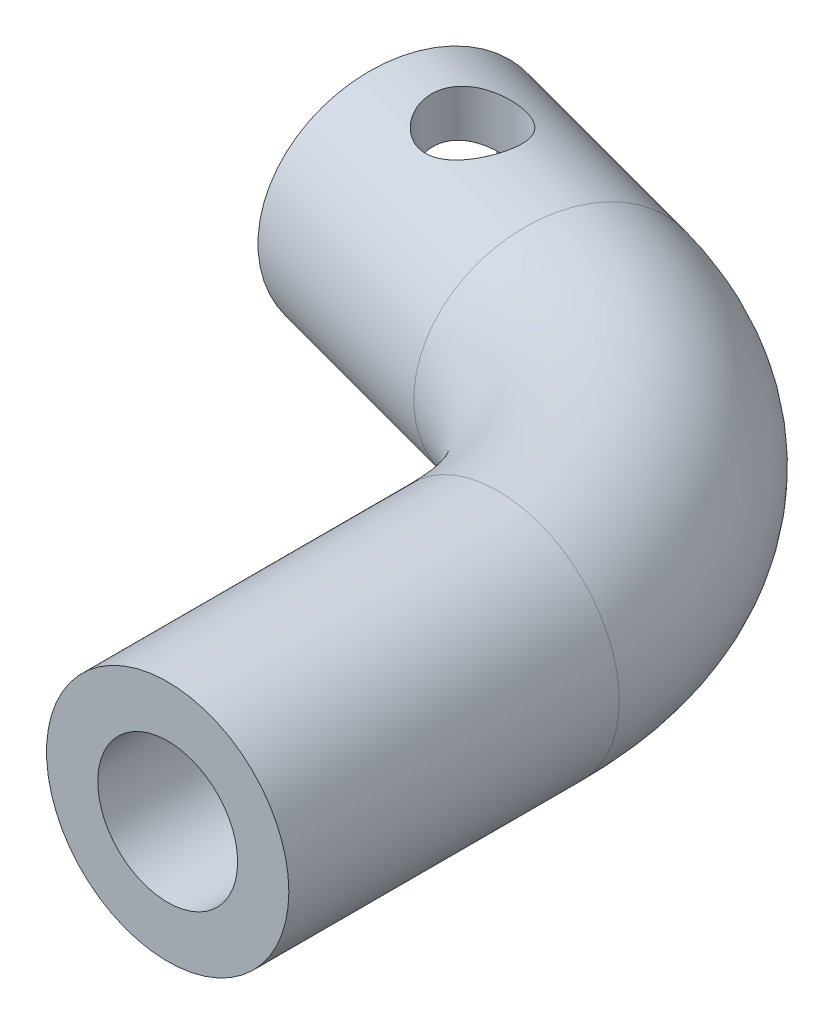
SolidWorks part; units mm, degrees
ref_plane "Front Plane" through (0, 0, 0) normal (0, 0, 1) x (1, 0, 0)
ref_plane "Top Plane" through (0, 0, 0) normal (0, 1, 0) x (1, 0, 0)
ref_plane "Right Plane" through (0, 0, 0) normal (1, 0, 0) x (0, 0, -1)
sketch "PROFILE" plane through (0, 0, 0) normal (0, 1, 0) x (1, 0, 0)
  line L0 (2.5, -10) -> (2.5, -25)
  line L1 (-7.0867, 2.4936) -> (-16.7459, 5.0818)
  line L2 (0, 0) -> (-28.2539, 0) construction
  arc A0 (2.5, -10) -> (-7.0867, 2.4936) centre (-10.4343, -10) ccw
  dimension "D1" = 15
  dimension "D2" = 10
  dimension "D3" = 2.5
  dimension "D4" = 17.5
  dimension "D5" = 15
  dimension "D6" = 25
ref_plane "Plane1" through (0, 0, 25) normal (0, 0, 1) x (1, 0, 0)
sketch "Sketch4" plane through (0, 0, 25) normal (0, 0, 1) x (1, 0, 0)
  circle A0 centre (2.5, 0) radius 5.5
  point P4 (0, 0)
  point P6 (0, 0)
  dimension "D1" = 11
sweep "Sweep2" add profiles "Sketch4" path "PROFILE"
sketch "Sketch6" plane through (0, 0, 25) normal (0, 0, 1) x (1, 0, 0)
  circle A0 centre (2.5, 0) radius 3.175
extrude "HOLE_SHAFT" cut sketch "Sketch6" against normal blind 10
sketch "Sketch7" plane through (-16.8946, 0, -4.5269) normal (-0.9659, 0, -0.2588) x (-0.2588, 0, 0.9659)
  line L0 (9.0122, 0) -> (-0.5744, 0) construction
  circle A0 centre (-0.5744, 0) radius 3.4
  point P3 (0, 0)
  point P4 (-0.5744, 0)
extrude "HOLE_POT" cut sketch "Sketch7" against normal blind 10
sketch "Sketch8" plane through (0, 0, 0) normal (0, 1, 0) x (1, 0, 0)
  line L0 (-7.0867, 2.4936) -> (-16.7459, 5.0818) construction
  circle A0 centre (-12.6435, 3.9825) radius 2
extrude "HOLE_INSERT" cut sketch "Sketch8" along normal through all
sketch "Sketch9" plane through (-7.2353, 0, -1.9387) normal (-0.9659, 0, -0.2588) x (-0.2588, 0, 0.9659)
  line L0 (-2.2229, 2.9736) -> (1.8712, -2.3619) construction
  line L1 (-2.2229, 2.9736) -> (2.4526, -1.5483)
  line L3 (-3.0167, 2.3654) -> (1.8712, -2.3619)
  line L5 (-0.5744, 0) -> (-4.9947, 0) construction
  circle A0 centre (-0.5744, 0) radius 3.4 construction
  arc A1 (-2.2229, 2.9736) -> (-3.0167, 2.3654) centre (-0.5744, 0) ccw
  arc A2 (1.8712, -2.3619) -> (2.4526, -1.5483) centre (-0.5744, 0) ccw
  dimension "D1" = 1
  dimension "D2" = 52.5
extrude "Boss-Extrude2" [suppressed] add sketch "Sketch9" along normal blind 1
sketch "Sketch11" plane through (-7.2353, 0, -1.9387) normal (-0.9659, 0, -0.2588) x (-0.2588, 0, 0.9659)
  line L0 (-0.9055, 3.3838) -> (0.7267, -3.1412)
  line L3 (-1.8756, 3.1412) -> (-0.2434, -3.3838)
  line L4 (-1.8756, 3.1412) -> (0.7267, -3.1412) construction
  line L5 (9.0122, 0) -> (-0.5744, 0) construction
  circle A0 centre (-0.5744, 0) radius 3.4 construction
  arc A1 (-0.2434, -3.3838) -> (0.7267, -3.1412) centre (-0.5744, 0) ccw
  arc A2 (-0.9055, 3.3838) -> (-1.8756, 3.1412) centre (-0.5744, 0) ccw
  dimension "D1" = 1
  dimension "D2" = 67.5
extrude "Boss-Extrude3" add sketch "Sketch11" along normal blind 1.5
